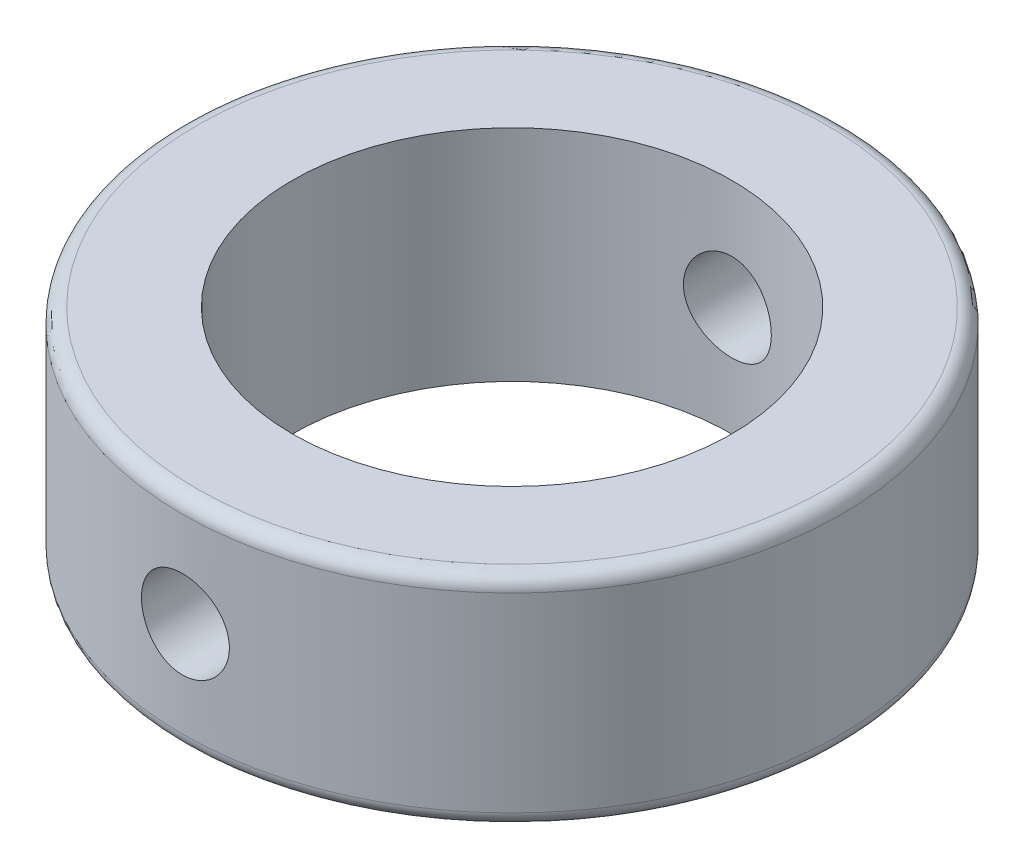
SolidWorks part; units mm, degrees
ref_plane "Front Plane" through (0, 0, 0) normal (0, 0, 1) x (1, 0, 0)
ref_plane "Top Plane" through (0, 0, 0) normal (0, 1, 0) x (1, 0, 0)
ref_plane "Right Plane" through (0, 0, 0) normal (1, 0, 0) x (0, 0, -1)
sketch "Sketch1" plane through (0, 0, 0) normal (0, 1, 0) x (1, 0, 0)
  circle A0 centre (0, 0) radius 22.5
  circle A1 centre (0, 0) radius 15
  dimension "D1" = 45
  dimension "D2" = 30
extrude "Boss-Extrude1" add sketch "Sketch1" along normal blind 15
sketch "Sketch2" plane through (0, 0, 0) normal (0, 0, 1) x (1, 0, 0)
  circle A0 centre (0, 7.5) radius 3
  point P2 (0, 0)
  dimension "D1" = 6
  dimension "D2" = 7.5
extrude "Cut-Extrude1" cut sketch "Sketch2" against normal through all both and the other way through all
fillet "Fillet1" radius 1 2 edges at (0, 0, 22.5) (0, 15, 22.5)
